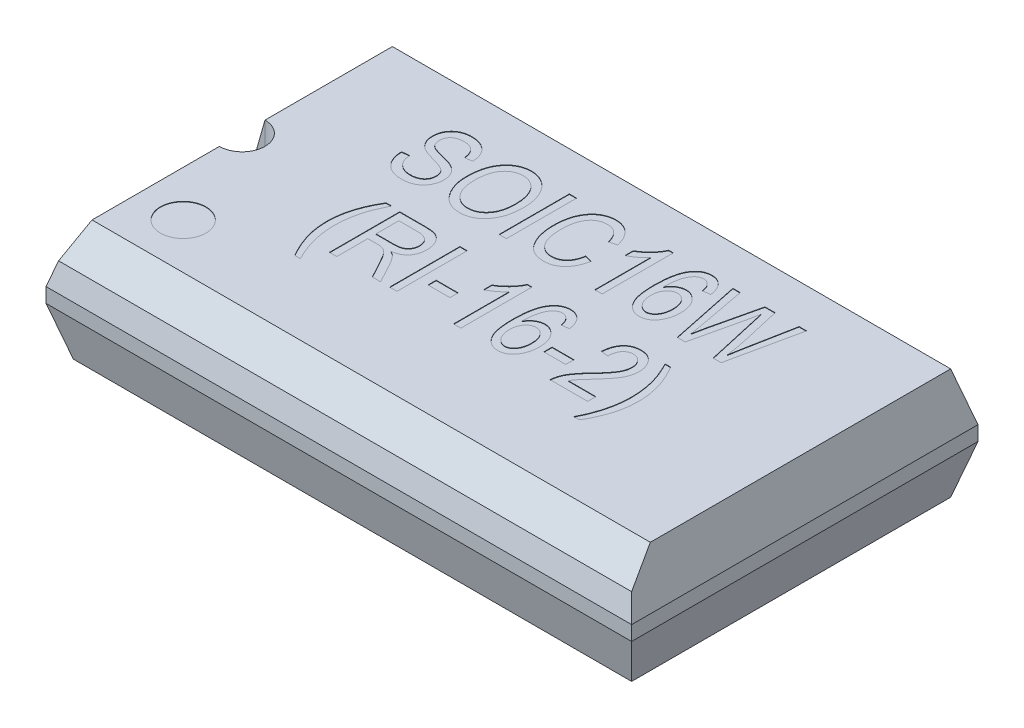
SolidWorks part; units mm, degrees
ref_plane "Front Plane" through (0, 0, 0) normal (0, 0, 1) x (1, 0, 0)
ref_plane "Top Plane" through (0, 0, 0) normal (0, 1, 0) x (1, 0, 0)
ref_plane "Right Plane" through (0, 0, 0) normal (1, 0, 0) x (0, 0, -1)
sketch "Sketch1" plane through (0, 0, 0) normal (0, 1, 0) x (1, 0, 0)
  line L1 (-6.425, 3.8) -> (6.425, 3.8)
  line L2 (-6.425, 3.8) -> (-6.425, -3.8)
  line L3 (-6.425, -3.8) -> (6.425, -3.8)
  line L4 (6.425, 3.8) -> (6.425, -3.8)
  line L5 (-6.425, 3.8) -> (6.425, -3.8) construction
  line L6 (-6.425, -3.8) -> (6.425, 3.8) construction
  point P0 (0, 0)
  dimension "D1" = 12.85
  dimension "D2" = 7.6
extrude "Boss-Extrude1" add sketch "Sketch1" along normal mid plane 2.44
chamfer "Chamfer1" distance 0.71 angle 45 1 edges at (0, 1.22, 3.8)
sketch "Sketch2" plane through (0, 0, -3.8) normal (0, 0, -1) x (-1, 0, 0)
  line L5 (-6.425, 1.22) -> (-6.125, 1.22)
  line L6 (-6.425, 1.22) -> (6.425, 1.22) construction
  line L7 (-6.125, 1.22) -> (-6.425, 0.16)
  line L8 (-6.425, 1.22) -> (-6.425, -1.22) construction
  line L9 (-6.425, 0.16) -> (-6.425, 1.22)
  line L10 (4.18, 0) -> (-4.18, 0) construction
  line L11 (-6.425, -1.22) -> (-6.125, -1.22)
  line L12 (-6.425, -1.22) -> (6.425, -1.22) construction
  line L13 (-6.125, -1.22) -> (-6.425, -0.16)
  line L14 (-6.425, -0.16) -> (-6.425, -1.22)
  line L15 (6.425, 1.22) -> (6.125, 1.22)
  line L16 (6.125, 1.22) -> (6.425, 0.16)
  line L17 (6.425, 1.22) -> (6.425, -1.22) construction
  line L18 (6.425, 0.16) -> (6.425, 1.22)
  line L19 (6.425, -1.22) -> (6.125, -1.22)
  line L20 (6.125, -1.22) -> (6.425, -0.16)
  line L21 (6.425, -0.16) -> (6.425, -1.22)
  dimension "D1" = 0.16
  dimension "D2" = 0.3
extrude "Cut-Extrude1" cut sketch "Sketch2" against normal through all
sketch "Sketch3" plane through (6.425, 0, 0) normal (1, 0, 0) x (0, 0, -1)
  line L0 (-3.8, -0.16) -> (-3.5, -1.22)
  line L2 (-3.8, -1.22) -> (3.8, -1.22) construction
  line L3 (-3.5, -1.22) -> (-3.8, -1.22)
  line L4 (-3.8, -1.22) -> (-3.8, -0.16)
  line L5 (3.8, -0.16) -> (3.8, -1.22)
  line L6 (3.8, -1.22) -> (3.5, -1.22)
  line L7 (3.5, -1.22) -> (3.8, -0.16)
  line L8 (3.8, 0.16) -> (3.8, 1.22)
  line L9 (3.8, 1.22) -> (3.5, 1.22)
  line L10 (-3.09, 1.22) -> (3.8, 1.22) construction
  line L11 (3.5, 1.22) -> (3.8, 0.16)
  line L12 (-3.8, 0.16) -> (-3.8, 1.22)
  line L13 (-3.8, 1.22) -> (-3.5, 1.22)
  line L14 (-3.5, 1.22) -> (-3.8, 0.16)
  dimension "D1" = 0.3
extrude "Cut-Extrude2" cut sketch "Sketch3" against normal through all
sketch "Sketch4" plane through (0, 1.22, 0) normal (0, 1, 0) x (1, 0, 0)
  line L0 (-6.125, -3.09) -> (-6.125, 3.5) construction
  line L1 (-6.125, -3.09) -> (6.125, -3.09) construction
  circle A0 centre (-5.125, -2.09) radius 0.5
  dimension "D3" = 1
  dimension "D1" = 1
  dimension "D2" = 1
extrude "Cut-Extrude3" cut sketch "Sketch4" against normal blind 0.01
sketch "Sketch5" plane through (0, 1.22, 0) normal (0, 1, 0) x (1, 0, 0)
  line L0 (-6.125, -3.09) -> (-6.125, 3.5) construction
  line L2 (-6.125, 0.705) -> (-8.125, 0.705)
  line L4 (-6.125, -0.295) -> (-8.125, -0.295)
  line L5 (-8.125, 0.705) -> (-8.125, -0.295)
  arc A0 (-6.125, -0.295) -> (-6.125, 0.705) centre (-6.125, 0.205) ccw
  dimension "D1" = 0.5
  dimension "D2" = 2
extrude "Cut-Extrude4" cut sketch "Sketch5" against normal blind 0.8
sketch "Sketch6" plane through (0, 1.22, 0) normal (0, 1, 0) x (1, 0, 0)
  line L0 (-4.125, 1.1) -> (4.125, 1.1) construction
  line L1 (-4.125, -1.1) -> (4.125, -1.1) construction
  line L2 (-6.125, 0.705) -> (-6.125, 3.5) construction
  line L3 (6.125, -3.09) -> (6.125, 3.5) construction
  line L4 (-6.125, 3.5) -> (6.125, 3.5) construction
  text T0 "SOIC16W" font "Arial Narrow" height in points 6
  text T1 " (RI-16-2)" font "Arial Narrow" height in points 6
  dimension "D1" = 2
  dimension "D2" = 2
  dimension "D3" = 2.4
  dimension "D4" = 2.2
extrude "Cut-Extrude5" cut sketch "Sketch6" against normal blind 0.01
